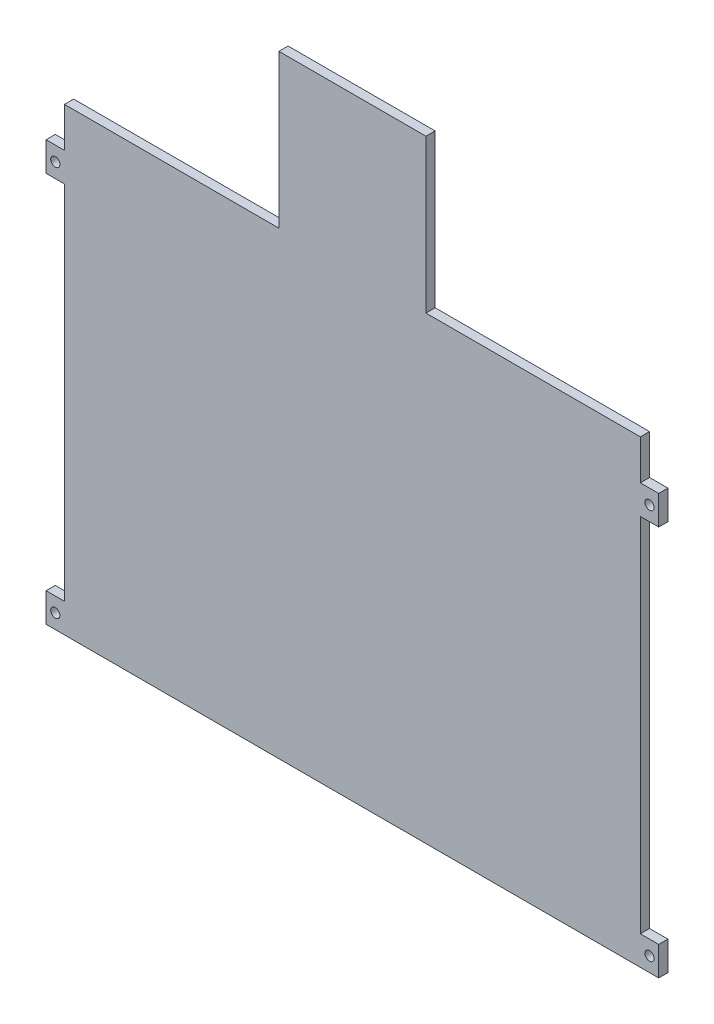
SolidWorks part; units mm, degrees
material "Balsa"
ref_plane "Plano frontal" through (0, 0, 0) normal (0, 0, 1) x (1, 0, 0)
ref_plane "Plano superior" through (0, 0, 0) normal (0, 1, 0) x (1, 0, 0)
ref_plane "Plano direito" through (0, 0, 0) normal (1, 0, 0) x (0, 0, -1)
sketch "Esboço1" plane through (0, 0, 0) normal (0, 0, 1) x (1, 0, 0)
  line L0 (0, 100) -> (0, 19.064) construction
  line L1 (-24, 100) -> (24, 100)
  line L2 (-94, 50) -> (-94, 37)
  line L3 (-94, -100) -> (94, -100)
  line L4 (94, 50) -> (94, 37)
  line L5 (-95.8764, 101.9962) -> (94, -100) construction
  line L6 (-94, -100) -> (97.7944, 104.0366) construction
  line L7 (-24, 100) -> (-24, 50)
  line L8 (-24, 50) -> (-94, 50)
  line L9 (24, 100) -> (24, 50)
  line L10 (24, 50) -> (94, 50)
  line L11 (94, -100) -> (100, -100)
  line L12 (100, -100) -> (100, -90.5)
  line L13 (100, -90.5) -> (94, -90.5)
  line L14 (94, -90.5) -> (100, -100) construction
  line L15 (94, 27.5) -> (100, 27.5)
  line L16 (100, 27.5) -> (100, 37)
  line L17 (100, 37) -> (94, 37)
  line L18 (94, 27.5) -> (94, -90.5)
  line L19 (94, 37) -> (100, 27.5) construction
  line L20 (-94, 37) -> (-100, 27.5) construction
  line L21 (-94, -90.5) -> (-100, -100) construction
  line L22 (-100, 37) -> (-94, 37)
  line L23 (-100, 27.5) -> (-100, 37)
  line L24 (-94, 27.5) -> (-100, 27.5)
  line L25 (-100, -90.5) -> (-94, -90.5)
  line L26 (-100, -100) -> (-100, -90.5)
  line L27 (-94, -100) -> (-100, -100)
  line L28 (-94, 27.5) -> (-94, -90.5)
  circle A0 centre (97, -95.25) radius 1.5
  circle A1 centre (97, 32.25) radius 1.5
  circle A2 centre (-97, 32.25) radius 1.5
  circle A3 centre (-97, -95.25) radius 1.5
  point P0 (0, 0)
  dimension "D8" = 3
  dimension "D1" = 188
  dimension "D2" = 200
  dimension "D3" = 70
  dimension "D4" = 50
  dimension "D5" = 100
  dimension "D6" = 6
  dimension "D7" = 9.5
  dimension "D9" = 118
  dimension "D10" = 9.5
extrude "Ressalto-extrusão1" add sketch "Esboço1" along normal blind 3
